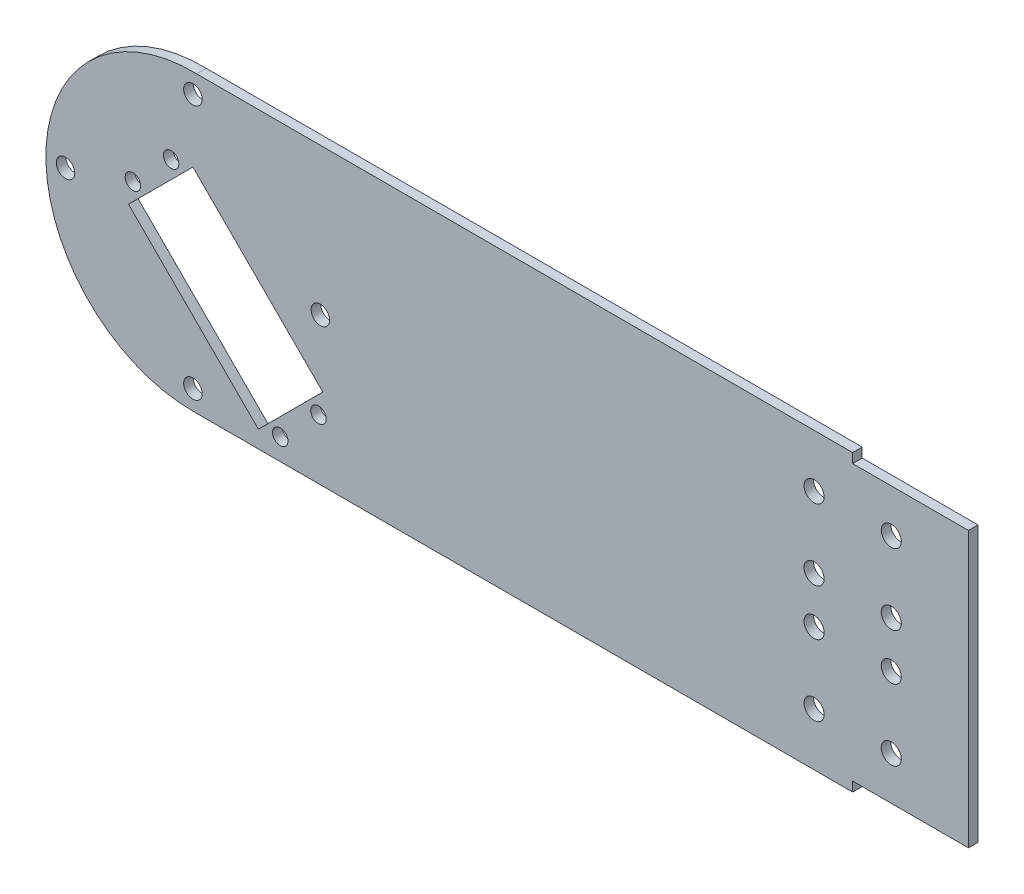
SolidWorks part; units mm, degrees
material "Teak"
ref_plane "Front Plane" through (0, 0, 0) normal (0, 0, 1) x (1, 0, 0)
ref_plane "Top Plane" through (0, 0, 0) normal (0, 1, 0) x (1, 0, 0)
ref_plane "Right Plane" through (0, 0, 0) normal (1, 0, 0) x (0, 0, -1)
other "Center of Mass"
sketch "Sketch1" plane through (0, 0, 0) normal (0, 0, 1) x (1, 0, 0)
  line L0 (0, 0) -> (0, -94.3086) construction
  line L1 (0, -47.625) -> (251.1969, -47.625)
  line L4 (251.1969, -47.625) -> (251.1969, 47.61)
  line L5 (251.1969, 47.61) -> (1.1969, 47.61)
  circle A0 centre (0, 0) radius 29.925 construction
  arc A1 (1.1969, 47.61) -> (0, -47.625) centre (0, 0) ccw
  circle A2 centre (0, -41.275) radius 3
  circle A3 centre (-41.275, 0) radius 3
  circle A4 centre (0, 41.275) radius 3
  circle A5 centre (41.275, 0) radius 3
  point P20 (0, 0)
  dimension "D1" = 59.85
  dimension "D2" = 47.625
  dimension "D3" = 6
  dimension "D5" = 82.55
  dimension "D6" = 0
  dimension "D8" = 250
  dimension "D4" = 4
extrude "Boss-Extrude1" add sketch "Sketch1" along normal blind 3.1
sketch "Sketch2" plane through (0, 0, 3.1) normal (0, 0, 1) x (1, 0, 0)
  line L0 (0, 38.275) -> (0, 36.6845)
  line L1 (-38.275, 0) -> (-37.3574, 0)
  line L2 (0, 0) -> (10.6066, -10.6066) construction
  line L3 (10.6066, -10.6066) -> (-0.2989, -21.5121) construction
  line L5 (21.2132, -42.0729) -> (42.0729, -21.2132)
  line L6 (21.2132, -42.0729) -> (-20.8597, 0)
  line L7 (-20.8597, 0) -> (0, 20.8597)
  line L8 (42.0729, -21.2132) -> (0, 20.8597)
  line L9 (21.2132, -42.0729) -> (0, 20.8597) construction
  line L10 (-20.8597, 0) -> (42.0729, -21.2132) construction
  circle A0 centre (-19.4454, 7.0711) radius 2.5
  circle A1 centre (-7.0711, 19.4454) radius 2.5
  circle A2 centre (40.6586, -28.2843) radius 2.5
  circle A3 centre (28.2843, -40.6586) radius 2.5
  circle A4 centre (0, 0) radius 2.1781 construction
  circle A5 centre (0, 41.275) radius 3 construction
  circle A6 centre (-41.275, 0) radius 3 construction
  dimension "D4" = 14.75
  dimension "D3" = 59.5
  dimension "D6" = 5
  dimension "D1" = 0
  dimension "D2" = 29.5
  dimension "D5" = 0
  dimension "D7" = 17.5
  dimension "D8" = 67.5
  dimension "D9" = 90
  dimension "D10" = 90
extrude "Cut-Extrude1" cut sketch "Sketch2" against normal through all contours A1 | L7 L8 L5 L6 | A2 | A3 | A0
sketch "Sketch3" plane through (0, 0, 3.1) normal (0, 0, 1) x (1, 0, 0)
  line L0 (251.1969, -47.625) -> (213.6969, -47.625)
  line L1 (251.1969, -47.625) -> (251.1969, -44.525)
  line L2 (213.6969, -47.625) -> (213.6969, -44.525)
  line L3 (251.1969, -44.525) -> (213.6969, -44.525)
  line L4 (0, -47.625) -> (251.1969, -47.625) construction
  line L6 (251.1969, -47.625) -> (251.1969, 47.61) construction
  dimension "D1" = 0
  dimension "D2" = 37.5
  dimension "D3" = 3.1
extrude "Cut-Extrude2" cut sketch "Sketch3" against normal through all
mirror "Mirror1" about plane through (0, 0, 0) normal (0, 1, 0) of "Cut-Extrude2"
sketch "Sketch7" plane through (0, 0, 3.1) normal (0, 0, 1) x (1, 0, 0)
  line L0 (251.1969, 0) -> (144.754, 0) construction
  line L1 (251.1969, -44.525) -> (251.1969, 44.525) construction
  line L2 (251.1969, -44.525) -> (213.6969, -44.525) construction
  line L3 (226.1969, -7.525) -> (226.1969, -30.525) construction
  line L4 (226.1969, 7.525) -> (226.1969, 30.525) construction
  line L5 (201.1969, -7.525) -> (201.1969, -30.525) construction
  line L6 (201.1969, 7.525) -> (201.1969, 30.525) construction
  circle A0 centre (226.1969, -30.525) radius 3.25
  circle A1 centre (226.1969, -7.525) radius 3.25
  circle A2 centre (226.1969, 7.525) radius 3.25
  circle A3 centre (226.1969, 30.525) radius 3.25
  circle A4 centre (201.1969, -30.525) radius 3.25
  circle A5 centre (201.1969, -7.525) radius 3.25
  circle A6 centre (201.1969, 7.525) radius 3.25
  circle A7 centre (201.1969, 30.525) radius 3.25
  dimension "D1" = 6.5
  dimension "D2" = 6.5
  dimension "D3" = 14
  dimension "D4" = 37
  dimension "D5" = 2
  dimension "D6" = 25
  dimension "D7" = 25
extrude "Cut-Extrude5" cut sketch "Sketch7" against normal through all
equation "\"thick\"= 3.1mm"
equation "\"small_bearing_outer\"=12.9mm"
equation "\"servo1_L\"=40.7mm"
equation "\"servo1_W\"=20.5mm"
equation "\"servo1_H\"=43.5mm"
equation "\"servo1_hL\"=49mm"
equation "\"servo1_hW\"=10mm"
equation "\"servo1_H2\"=27mm"
equation "\"large_bearing_inner\"=2.75in"
equation "\"large_bearing_outer\"=4.75in"
equation "\"large_bearing_thick\"=3/8in"
equation "\"large_bearing_h1\"=3.25in"
equation "\"large_bearing_h2\"=4.25in"
equation "\"D1@Sketch1\"=\"large_bearing_inner\"-10"
equation "\"D2@Sketch1\"=(\"large_bearing_inner\"+\"large_bearing_outer\")/4"
equation "\"D5@Sketch1\"=\"large_bearing_h1\""
equation "\"D1@Boss-Extrude1\"=\"thick\""
equation "\"D2@Sketch2\"=\"servo2_W\""
equation "\"D3@Sketch2\"=\"servo2_L\""
equation "\"D4@Sketch2\"=\"D2@Sketch2\"/2"
equation "\"D7@Sketch2\"=\"servo2_hW\""
equation "\"D8@Sketch2\"=\"servo2_hL\""
equation "\"D2@Sketch3\"=75/2"
equation "\"D3@Sketch3\"=\"thick\""
equation "\"servo2_L\"=59.5mm"
equation "\"servo2_W\"=29.5mm"
equation "\"servo2_hL\"=67.5mm"
equation "\"servo2_hW\"=17.5mm"
